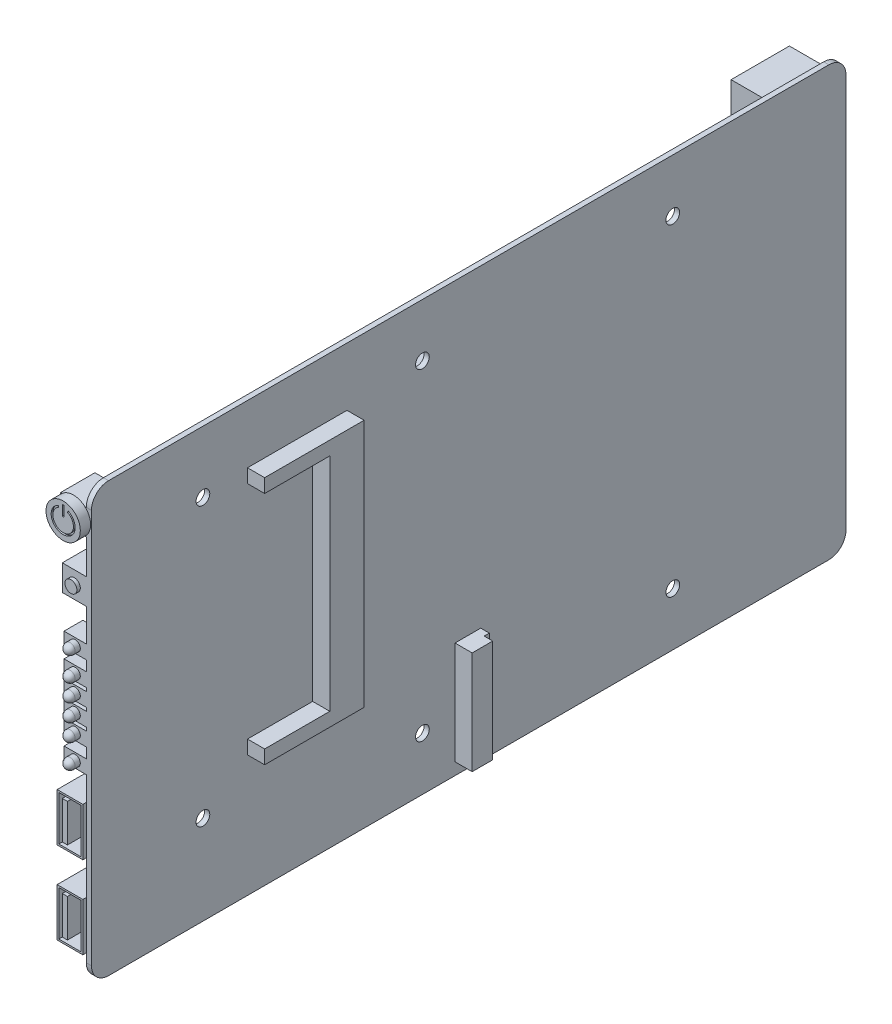
SolidWorks part; units mm, degrees
ref_plane "前视基准面" through (0, 0, 0) normal (0, 0, 1) x (1, 0, 0)
ref_plane "上视基准面" through (0, 0, 0) normal (0, 1, 0) x (1, 0, 0)
ref_plane "右视基准面" through (0, 0, 0) normal (1, 0, 0) x (0, 0, -1)
sketch "草图1" plane through (0, 0, 0) normal (1, 0, 0) x (0, 0, -1)
  line L1 (110, 62.5) -> (-110, 62.5)
  line L2 (110, 62.5) -> (110, -62.5)
  line L3 (110, -62.5) -> (-110, -62.5)
  line L4 (-110, 62.5) -> (-110, -62.5)
  line L5 (110, 62.5) -> (-110, -62.5) construction
  line L6 (110, -62.5) -> (-110, 62.5) construction
  point P0 (0, 0)
  dimension "D1" = 220
  dimension "D2" = 125
extrude "凸台-拉伸1" add sketch "草图1" against normal blind 1.5
fillet "圆角1" radius 5 4 edges at (-0.75, -62.5, -110) (-0.75, -62.5, 110) (-0.75, 62.5, -110) (-0.75, 62.5, 110)
sketch "草图2" plane through (0, 0, 0) normal (1, 0, 0) x (0, 0, -1)
  line L4 (58, -27.5) -> (58, -60.5) construction
  line L5 (-105, -62.5) -> (105, -62.5) construction
  line L7 (-73, 48.5) -> (-35.5, 48.5) construction
  line L8 (-73, 48.5) -> (-73, -30) construction
  line L9 (-73, -30) -> (-35.5, -30) construction
  line L10 (-35.5, 48.5) -> (-35.5, -30) construction
  line L11 (-73, 48.5) -> (-35.5, -30) construction
  line L12 (-73, -30) -> (-35.5, 48.5) construction
  line L13 (-110, 57.5) -> (-110, -57.5) construction
  line L14 (105, 62.5) -> (-105, 62.5) construction
  line L15 (-35.5, 45.5) -> (-64.5, 45.5)
  line L16 (-64.5, 45.5) -> (-64.5, 41.5)
  line L17 (-64.5, 41.5) -> (-45.5, 41.5)
  line L18 (-45.5, 41.5) -> (-45.5, -23)
  line L19 (-45.5, -23) -> (-64.5, -23)
  line L20 (-64.5, -23) -> (-64.5, -27)
  line L21 (-64.5, -27) -> (-35.5, -27)
  line L22 (-35.5, -27) -> (-35.5, 45.5)
  line L23 (-5.5, -27.5) -> (-5.5, -60.5) construction
  line L25 (-5.5, -27.5) -> (58, -27.5) construction
  line L26 (-5.5, -60.5) -> (58, -60.5) construction
  line L32 (-4, -29) -> (3.5, -29)
  line L33 (-4, -29) -> (-4, -59)
  line L34 (-4, -59) -> (3.5, -59)
  line L35 (3.5, -29) -> (3.5, -59)
  point P0 (10.5, -44)
  point P5 (-54.25, 9.25)
  dimension "D1" = 33
  dimension "D3" = 1.5
  dimension "D4" = 1.5
  dimension "D5" = 37.5
  dimension "D6" = 37
  dimension "D7" = 14
  dimension "D8" = 78.5
  dimension "D9" = 3
  dimension "D10" = 4
  dimension "D11" = 4
  dimension "D12" = 3
  dimension "D13" = 29
  dimension "D14" = 10
  dimension "D15" = 1.5
  dimension "D16" = 104.5
  dimension "D17" = 3.5
  dimension "D20" = 7.5
extrude "凸台-拉伸2" add sketch "草图2" along normal blind 5
sketch "草图29" plane through (5, 0, 0) normal (1, 0, 0) x (0, 0, -1)
  line L0 (-4, -59) -> (3.5, -59) construction
  line L1 (3.5, -29) -> (2, -29)
  line L2 (3.5, -29) -> (3.5, -59)
  line L3 (3.5, -59) -> (2, -59)
  line L4 (2, -29) -> (2, -59)
  dimension "D1" = 1.5
extrude "切除-拉伸13" cut sketch "草图29" against normal blind 2.5
sketch "草图5" plane through (0, 0, 0) normal (1, 0, 0) x (0, 0, -1)
  line L0 (-110, 57.5) -> (-110, -57.5) construction
  line L1 (105, 62.5) -> (-105, 62.5) construction
  line L2 (-77.5, 44.5) -> (-77.5, 19.9461) construction
  line L3 (59.5, 47) -> (59.5, 24.1556) construction
  line L4 (-13.5, 47) -> (-13.5, 25.5172) construction
  circle A0 centre (-77.5, 44.5) radius 2
  circle A1 centre (-77.5, -36.5) radius 2
  circle A2 centre (59.5, 47) radius 2
  circle A3 centre (59.5, -47) radius 2
  circle A4 centre (-13.5, 47) radius 2
  circle A5 centre (-13.5, -47) radius 2
  dimension "D1" = 4
  dimension "D6" = 137
  dimension "D2" = 32.5
  dimension "D3" = 18
  dimension "D4" = 81
  dimension "D5" = 15.5
  dimension "D7" = 94
  dimension "D8" = 15.5
  dimension "D9" = 94
  dimension "D10" = 73
extrude "切除-拉伸2" cut sketch "草图5" against normal through all
sketch "草图6" plane through (-1.5, 0, 0) normal (-1, 0, 0) x (0, 0, 1)
  line L0 (-105, 62.5) -> (105, 62.5) construction
  line L1 (-47.5, 42.5) -> (35, 42.5)
  line L2 (-47.5, 42.5) -> (-47.5, -21)
  line L3 (-47.5, -21) -> (35, -21)
  line L4 (35, 42.5) -> (35, -21)
  line L5 (110, 57.5) -> (110, -57.5) construction
  dimension "D1" = 20
  dimension "D2" = 63.5
  dimension "D3" = 82.5
  dimension "D4" = 75
extrude "凸台-拉伸4" add sketch "草图6" along normal blind 18
fillet "圆角2" radius 1 2 edges at (-19.5, 10.75, -47.5) (-19.5, 10.75, 35)
sketch "草图7" plane through (-19.5, 0, 0) normal (-1, 0, 0) x (0, 0, 1)
  line L0 (-47.5, 42.5) -> (-47.5, -21) construction
  line L1 (-47.5, -17.5) -> (35, -17.5)
  line L2 (-47.5, -17.5) -> (-47.5, -20)
  line L3 (-47.5, -20) -> (35, -20)
  line L4 (35, -17.5) -> (35, -20)
  line L5 (35, -21) -> (35, 42.5) construction
  line L6 (-47.5, -21) -> (35, -21) construction
  dimension "D1" = 1
  dimension "D2" = 2.5
extrude "切除-拉伸3" cut sketch "草图7" against normal blind 10
pattern_linear "阵列(线性)1" count 18 spacing 3.4 along (0, 1, 0) of "切除-拉伸3"
sketch "草图8" plane through (-19.5, 0, 0) normal (-1, 0, 0) x (0, 0, 1)
  line L0 (35, 42.5) -> (-47.5, 42.5) construction
  line L1 (-31.5, 42.5) -> (-30, 42.5)
  line L2 (-31.5, 42.5) -> (-31.5, -21)
  line L3 (-31.5, -21) -> (-30, -21)
  line L4 (-30, 42.5) -> (-30, -21)
  line L5 (-46.5, -21) -> (34, -21) construction
  line L6 (-47.5, -17.5) -> (-47.5, -20) construction
  dimension "D1" = 1.5
  dimension "D2" = 16
extrude "切除-拉伸4" cut sketch "草图8" against normal blind 10
pattern_linear "阵列(线性)2" count 5 spacing 11 along (0, 0, 1) of "切除-拉伸4"
sketch "草图9" plane through (-1.5, 0, 0) normal (-1, 0, 0) x (0, 0, 1)
  line L0 (105, -62.5) -> (-105, -62.5) construction
  line L1 (-75.5, 0.5) -> (-66.5, 0.5) construction
  line L2 (-75.5, 0.5) -> (-75.5, -40.5) construction
  line L3 (-75.5, -40.5) -> (-66.5, -40.5) construction
  line L4 (-66.5, 0.5) -> (-66.5, -40.5) construction
  line L5 (-110, -57.5) -> (-110, 57.5) construction
  line L7 (-75.5, -40.5) -> (-66.75, -40.5)
  line L8 (-75.5, -40.5) -> (-75.5, -1.5)
  line L9 (-75.5, -1.5) -> (-66.75, -1.5)
  line L10 (-66.75, -40.5) -> (-66.75, -1.5)
  dimension "D1" = 22
  dimension "D2" = 41
  dimension "D3" = 9
  dimension "D4" = 34.5
  dimension "D5" = 0.5
  dimension "D6" = 2
extrude "凸台-拉伸5" add sketch "草图9" along normal blind 11
sketch "草图10" plane through (-12.5, 0, 0) normal (-1, 0, 0) x (0, 0, 1)
  line L0 (-66.75, -1.5) -> (-75.5, -1.5) construction
  line L1 (-72.5, -27) -> (-70.5, -27)
  line L2 (-72.5, -27) -> (-72.5, -38.5)
  line L3 (-72.5, -38.5) -> (-70.5, -38.5)
  line L4 (-70.5, -27) -> (-70.5, -38.5)
  line L5 (-72.5, -3.5) -> (-70.5, -3.5)
  line L6 (-72.5, -3.5) -> (-72.5, -25.5)
  line L7 (-72.5, -25.5) -> (-70.5, -25.5)
  line L8 (-70.5, -3.5) -> (-70.5, -25.5)
  line L9 (-75.5, -1.5) -> (-75.5, -40.5) construction
  dimension "D1" = 11.5
  dimension "D2" = 22
  dimension "D3" = 2
  dimension "D4" = 1.5
  dimension "D5" = 3
  dimension "D6" = 2
extrude "切除-拉伸5" cut sketch "草图10" against normal blind 7.5
sketch "草图11" plane through (-1.5, 0, 0) normal (-1, 0, 0) x (0, 0, 1)
  line L0 (-110, -57.5) -> (-110, 57.5) construction
  line L1 (-110, 56.5) -> (-93, 56.5)
  line L2 (-110, 56.5) -> (-110, 42.5)
  line L3 (-110, 42.5) -> (-93, 42.5)
  line L4 (-93, 56.5) -> (-93, 42.5)
  line L5 (-105, 62.5) -> (105, 62.5) construction
  dimension "D1" = 6
  dimension "D2" = 14
  dimension "D3" = 17
extrude "凸台-拉伸6" add sketch "草图11" along normal blind 15
sketch "草图12" plane through (0, 0, -110) normal (0, 0, -1) x (-1, 0, 0)
  line L0 (16.5, 56.5) -> (16.5, 42.5) construction
  line L1 (10.5, 56) -> (16, 56)
  line L2 (10.5, 56) -> (10.5, 43)
  line L3 (10.5, 43) -> (16, 43)
  line L4 (16, 56) -> (16, 43)
  line L5 (2, 56) -> (7.5, 56)
  line L6 (2, 56) -> (2, 43)
  line L7 (2, 43) -> (7.5, 43)
  line L8 (7.5, 56) -> (7.5, 43)
  line L9 (13.5, 55) -> (15, 55)
  line L10 (13.5, 55) -> (13.5, 44)
  line L11 (13.5, 44) -> (15, 44)
  line L12 (15, 55) -> (15, 44)
  line L13 (5, 55) -> (6.5, 55)
  line L14 (5, 55) -> (5, 44)
  line L15 (5, 44) -> (6.5, 44)
  line L16 (6.5, 55) -> (6.5, 44)
  line L17 (16.5, 56.5) -> (1.5, 56.5) construction
  line L18 (16.5, 42.5) -> (1.5, 42.5) construction
  dimension "D1" = 0.5
  dimension "D2" = 0.5
  dimension "D3" = 1
  dimension "D4" = 1
  dimension "D5" = 1
  dimension "D6" = 1
  dimension "D7" = 1.5
  dimension "D8" = 3
  dimension "D9" = 0.5
  dimension "D10" = 14
extrude "切除-拉伸6" cut sketch "草图12" against normal blind 10
sketch "草图13" plane through (-1.5, 0, 0) normal (-1, 0, 0) x (0, 0, 1)
  line L0 (-110, -57.5) -> (-110, 42.5) construction
  line L1 (-110, 32) -> (-94, 32)
  line L2 (-110, 32) -> (-110, 15.5)
  line L3 (-110, 15.5) -> (-94, 15.5)
  line L4 (-94, 32) -> (-94, 15.5)
  line L5 (-110, 42.5) -> (-93, 42.5) construction
  dimension "D1" = 16
  dimension "D2" = 16.5
  dimension "D3" = 10.5
extrude "凸台-拉伸7" add sketch "草图13" along normal blind 13.5
sketch "草图14" plane through (0, 0, -110) normal (0, 0, -1) x (-1, 0, 0)
  line L0 (11, 20.75) -> (11, 17.5)
  line L1 (3.5, 30) -> (11, 30)
  line L2 (3.5, 30) -> (3.5, 17.5)
  line L3 (3.5, 17.5) -> (11, 17.5)
  line L4 (11, 30) -> (11, 26.75)
  line L5 (11, 26.75) -> (14, 26.75)
  line L7 (11, 20.75) -> (14, 20.75)
  line L8 (14, 26.75) -> (14, 20.75)
  line L9 (15, 32) -> (15, 15.5) construction
  line L10 (15, 15.5) -> (1.5, 15.5) construction
  line L11 (15, 32) -> (1.5, 32) construction
  line L12 (1.5, 42.5) -> (1.5, -21) construction
  line L13 (3.5, 23.75) -> (24.5, 23.75) construction
  point P18 (14, 23.75)
  dimension "D1" = 4
  dimension "D2" = 2
  dimension "D3" = 2
  dimension "D4" = 2
  dimension "D5" = 1
  dimension "D6" = 6
extrude "切除-拉伸7" cut sketch "草图14" against normal blind 13.5
pattern_linear "阵列(线性)3" count 2 spacing 20.5 along (0, -1, 0) of "凸台-拉伸7", "切除-拉伸7"
sketch "草图15" plane through (-1.5, 0, 0) normal (-1, 0, 0) x (0, 0, 1)
  line L1 (-111, -16) -> (-98, -16)
  line L2 (-111, -16) -> (-111, -31)
  line L3 (-111, -31) -> (-98, -31)
  line L4 (-98, -16) -> (-98, -31)
  line L5 (-110, -5) -> (-94, -5) construction
  line L7 (-110, -57.5) -> (-110, -5) construction
  dimension "D1" = 11
  dimension "D2" = 15
  dimension "D3" = 13
  dimension "D4" = 1
extrude "凸台-拉伸8" add sketch "草图15" along normal blind 6
sketch "草图16" plane through (0, 0, -111) normal (0, 0, -1) x (-1, 0, 0)
  line L0 (4, -16.5) -> (7, -16.5)
  line L1 (7, -16.5) -> (7, -30.5)
  line L2 (7, -30.5) -> (4, -30.5)
  line L3 (4, -30.5) -> (2, -28.5)
  line L4 (2, -28.5) -> (2, -18.5)
  line L5 (2, -18.5) -> (4, -16.5)
  line L6 (7.5, -16) -> (7.5, -31) construction
  line L7 (7.5, -16) -> (1.5, -16) construction
  line L8 (1.5, -16) -> (1.5, -31) construction
  line L9 (7, -23.5) -> (5.1736, -23.5) construction
  line L10 (7.5, -31) -> (1.5, -31) construction
  line L12 (4, -18.5) -> (5, -18.5)
  line L13 (4, -18.5) -> (4, -28.5)
  line L14 (4, -28.5) -> (5, -28.5)
  line L15 (5, -18.5) -> (5, -28.5)
  point P12 (1.5, -23.5)
  dimension "D1" = 0.5
  dimension "D2" = 0.5
  dimension "D3" = 0.5
  dimension "D4" = 0.5
  dimension "D5" = 135
  dimension "D6" = 10
  dimension "D7" = 1
  dimension "D8" = 10
extrude "切除-拉伸8" cut sketch "草图16" against normal blind 7.5
sketch "草图17" plane through (0, 0, -111) normal (0, 0, -1) x (-1, 0, 0)
  line L1 (4, -18.5) -> (5, -18.5)
  line L2 (4, -18.5) -> (4, -28.5)
  line L3 (4, -28.5) -> (5, -28.5)
  line L4 (5, -18.5) -> (5, -28.5)
extrude "切除-拉伸9" cut sketch "草图17" against normal blind 2
sketch "草图18" plane through (-1.5, 0, 0) normal (-1, 0, 0) x (0, 0, 1)
  line L0 (-110, -57.5) -> (-110, -31) construction
  line L1 (-110, -42) -> (-97, -42)
  line L2 (-110, -42) -> (-110, -52)
  line L3 (-110, -52) -> (-97, -52)
  line L4 (-97, -42) -> (-97, -52)
  line L5 (-111, -31) -> (-98, -31) construction
  dimension "D1" = 11
  dimension "D2" = 10
  dimension "D3" = 13
extrude "凸台-拉伸9" add sketch "草图18" along normal blind 10
sketch "草图19" plane through (0, 0, -110) normal (0, 0, -1) x (-1, 0, 0)
  line L0 (11.5, -47) -> (2.6141, -47) construction
  line L1 (11.5, -42) -> (11.5, -52) construction
  line L2 (6.5, -42) -> (6.5, -51.1185) construction
  line L3 (11.5, -42) -> (1.5, -42) construction
  circle A0 centre (6.5, -47) radius 3
  circle A1 centre (6.5, -47) radius 1
  dimension "D1" = 6
  dimension "D2" = 2
extrude "切除-拉伸10" cut sketch "草图19" against normal blind 10
fillet "圆角3" radius 1 1 edges at (-6.5, -46, -110)
sketch "草图20" plane through (-1.5, 0, 0) normal (-1, 0, 0) x (0, 0, 1)
  line L0 (105, -62.5) -> (-105, -62.5) construction
  line L1 (111, -41) -> (94.5, -41)
  line L2 (111, -41) -> (111, -55)
  line L3 (111, -55) -> (94.5, -55)
  line L4 (94.5, -41) -> (94.5, -55)
  line L5 (110, 57.5) -> (110, -57.5) construction
  dimension "D1" = 7.5
  dimension "D2" = 14
  dimension "D3" = 1
  dimension "D4" = 16.5
extrude "凸台-拉伸10" add sketch "草图20" along normal blind 7.5
sketch "草图21" plane through (0, 0, 111) normal (0, 0, 1) x (1, 0, 0)
  line L0 (-9, -55) -> (-9, -41) construction
  line L1 (-8.5, -41.5) -> (-2, -41.5)
  line L2 (-8.5, -41.5) -> (-8.5, -54.5)
  line L3 (-8.5, -54.5) -> (-2, -54.5)
  line L4 (-2, -41.5) -> (-2, -54.5)
  line L5 (-7.5, -42.5) -> (-6, -42.5)
  line L6 (-7.5, -42.5) -> (-7.5, -53.5)
  line L7 (-7.5, -53.5) -> (-6, -53.5)
  line L8 (-6, -42.5) -> (-6, -53.5)
  line L9 (-9, -55) -> (-1.5, -55) construction
  line L10 (-9, -41) -> (-1.5, -41) construction
  line L11 (-1.5, -55) -> (-1.5, -57.5) construction
  dimension "D1" = 0.5
  dimension "D2" = 0.5
  dimension "D3" = 0.5
  dimension "D4" = 1
  dimension "D5" = 1
  dimension "D6" = 1
  dimension "D7" = 1.5
  dimension "D8" = 0.5
extrude "切除-拉伸11" cut sketch "草图21" against normal blind 13
pattern_linear "阵列(线性)4" count 2 spacing 24 along (0, 1, 0) of "凸台-拉伸10", "切除-拉伸11"
sketch "草图22" plane through (-1.5, 0, 0) normal (-1, 0, 0) x (0, 0, 1)
  line L0 (110, 57.5) -> (110, -17) construction
  line L1 (100, 57.5) -> (110, 57.5)
  line L2 (100, 57.5) -> (100, 50)
  line L3 (100, 50) -> (110, 50)
  line L4 (110, 57.5) -> (110, 50)
  line L5 (-105, 62.5) -> (105, 62.5) construction
  dimension "D1" = 10
  dimension "D2" = 7.5
  dimension "D3" = 5
extrude "凸台-拉伸11" add sketch "草图22" along normal blind 7.5
sketch "草图23" plane through (0, 0, 110) normal (0, 0, 1) x (1, 0, 0)
  line L0 (-9, 53.75) -> (11.7049, 53.75) construction
  line L1 (-9, 50) -> (-9, 57.5) construction
  line L2 (-5.25, 50) -> (-5.25, 59.3543) construction
  line L3 (-9, 50) -> (-1.5, 50) construction
  circle A0 centre (-5.25, 53.75) radius 5
  dimension "D1" = 10
extrude "凸台-拉伸12" add sketch "草图23" along normal blind 3
sketch "草图24" plane through (0, 0, 113) normal (0, 0, 1) x (1, 0, 0)
  line L0 (-5.25, 53.75) -> (-5.25, 59.5272) construction
  line L1 (-5.25, 53.75) -> (-6.9416, 57.3776) construction
  line L2 (-5.5, 57.75) -> (-5, 57.75)
  line L3 (-5.5, 57.75) -> (-5.5, 54.75)
  line L4 (-5.5, 54.75) -> (-5, 54.75)
  line L5 (-5, 57.75) -> (-5, 54.75)
  line L6 (-5.25, 53.75) -> (-3.6383, 57.2064) construction
  line L7 (-6.7292, 56.9221) -> (-6.5179, 56.4689)
  line L8 (-3.7708, 56.9221) -> (-3.9821, 56.4689)
  arc A0 (-6.5179, 56.4689) -> (-3.9821, 56.4689) centre (-5.25, 53.75) ccw
  circle A1 centre (-5.25, 53.75) radius 5 construction
  arc A2 (-6.7292, 56.9221) -> (-3.7708, 56.9221) centre (-5.25, 53.75) ccw
  dimension "D1" = 6
  dimension "D2" = 7
  dimension "D3" = 50
  dimension "D4" = 0.5
  dimension "D5" = 3
  dimension "D6" = 1
extrude "切除-拉伸12" cut sketch "草图24" against normal blind 0.5
sketch "草图25" plane through (-1.5, 0, 0) normal (-1, 0, 0) x (0, 0, 1)
  line L0 (110, 50) -> (110, -17) construction
  line L1 (110, 40) -> (103, 40)
  line L2 (110, 40) -> (110, 32.5)
  line L3 (110, 32.5) -> (103, 32.5)
  line L4 (103, 40) -> (103, 32.5)
  line L5 (100, 50) -> (110, 50) construction
  dimension "D1" = 7.5
  dimension "D2" = 7
  dimension "D3" = 10
extrude "凸台-拉伸13" add sketch "草图25" along normal blind 7
sketch "草图26" plane through (0, 0, 110) normal (0, 0, 1) x (1, 0, 0)
  line L0 (-5, 40) -> (-5, 39.3156) construction
  line L1 (-8.5, 40) -> (-1.5, 40) construction
  line L2 (-8.5, 36.25) -> (-7.3359, 36.25) construction
  line L3 (-8.5, 32.5) -> (-8.5, 40) construction
  circle A0 centre (-5, 36.25) radius 1.75
  dimension "D1" = 3.5
extrude "凸台-拉伸14" add sketch "草图26" along normal blind 1
sketch "草图27" plane through (-1.5, 0, 0) normal (-1, 0, 0) x (0, 0, 1)
  line L0 (110, 32.5) -> (110, -17) construction
  line L1 (110, -6) -> (104.5, -6)
  line L2 (110, -6) -> (110, -10)
  line L3 (110, -10) -> (104.5, -10)
  line L4 (104.5, -6) -> (104.5, -10)
  line L5 (111, -17) -> (94.5, -17) construction
  line L7 (110, -3) -> (104.5, -3)
  line L8 (110, -3) -> (110, 1)
  line L9 (110, 1) -> (104.5, 1)
  line L10 (104.5, -3) -> (104.5, 1)
  line L11 (110, 6) -> (104.5, 6)
  line L12 (110, 6) -> (110, 2)
  line L13 (110, 2) -> (104.5, 2)
  line L14 (104.5, 6) -> (104.5, 2)
  line L15 (110, 11) -> (104.5, 11)
  line L16 (110, 11) -> (110, 7)
  line L17 (110, 7) -> (104.5, 7)
  line L18 (104.5, 11) -> (104.5, 7)
  line L19 (110, 16) -> (104.5, 16)
  line L20 (110, 16) -> (110, 12)
  line L21 (110, 12) -> (104.5, 12)
  line L22 (104.5, 16) -> (104.5, 12)
  line L23 (110, 23) -> (104.5, 23)
  line L24 (110, 23) -> (110, 19)
  line L25 (110, 19) -> (104.5, 19)
  line L26 (104.5, 23) -> (104.5, 19)
  point P28 (107.25, 11)
  dimension "D1" = 5.5
  dimension "D2" = 4
  dimension "D3" = 7
  dimension "D4" = 3
  dimension "D5" = 1
  dimension "D6" = 1
  dimension "D7" = 1
  dimension "D8" = 3
extrude "凸台-拉伸15" add sketch "草图27" along normal blind 6.5
sketch "草图28" plane through (0, 0, 110) normal (0, 0, 1) x (1, 0, 0)
  line L0 (-4.75, -10) -> (-4.75, -12.9971) construction
  line L1 (-8, -10) -> (-1.5, -10) construction
  line L2 (-8, -8) -> (-9.235, -8) construction
  line L3 (-8, -10) -> (-8, -6) construction
  line L4 (-8, -1) -> (-9.0138, -1) construction
  line L5 (-8, -3) -> (-8, 1) construction
  line L6 (-8, 4) -> (-9.0138, 4) construction
  line L8 (-8, 2) -> (-8, 6) construction
  line L9 (-8, 9) -> (-10.4407, 9) construction
  line L10 (-8, 7) -> (-8, 11) construction
  line L11 (-8, 14) -> (-8.8504, 14) construction
  line L12 (-8, 12) -> (-8, 16) construction
  line L13 (-8, 21) -> (-9.0138, 21) construction
  line L14 (-8, 19) -> (-8, 23) construction
  circle A0 centre (-4.75, -8) radius 1.5
  circle A1 centre (-4.75, -1) radius 1.5
  circle A2 centre (-4.75, 4) radius 1.5
  circle A3 centre (-4.75, 9) radius 1.5
  circle A4 centre (-4.75, 14) radius 1.5
  circle A5 centre (-4.75, 21) radius 1.5
  dimension "D1" = 3
extrude "凸台-拉伸16" add sketch "草图28" along normal blind 3
fillet "圆角4" radius 1.5 6 edges at (-3.25, 21, 113) (-3.25, 14, 113) (-3.25, 9, 113) (-3.25, 4, 113) (-3.25, -1, 113) (-3.25, -8, 113)
